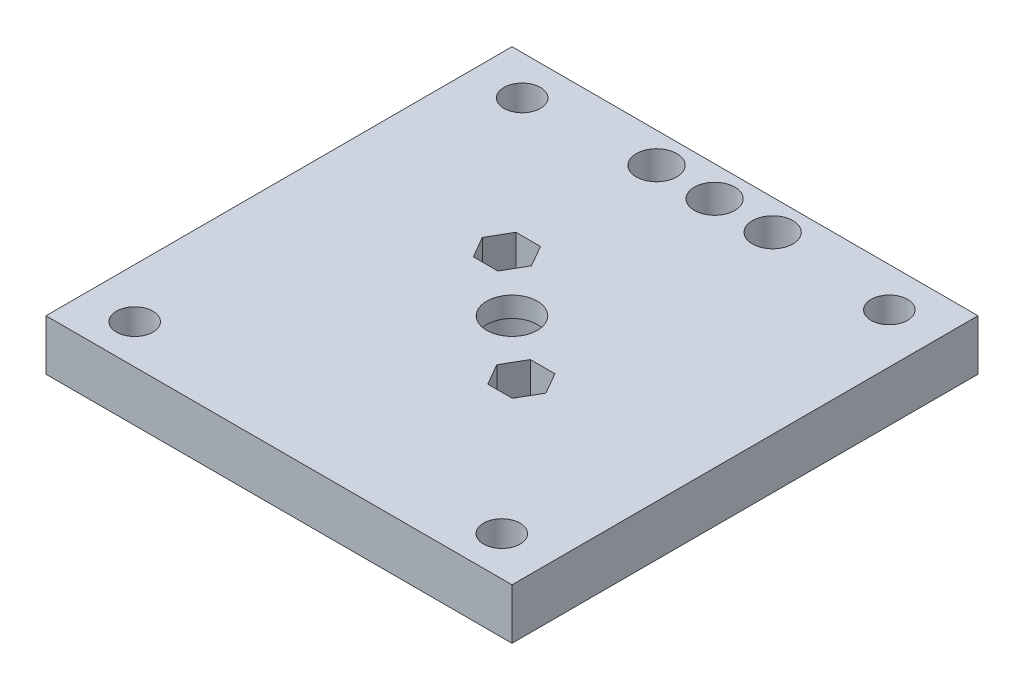
SolidWorks part; units mm, degrees
ref_plane "Front Plane" through (0, 0, 0) normal (0, 0, 1) x (1, 0, 0)
ref_plane "Top Plane" through (0, 0, 0) normal (0, 1, 0) x (1, 0, 0)
ref_plane "Right Plane" through (0, 0, 0) normal (1, 0, 0) x (0, 0, -1)
sketch "Sketch2" plane through (0, 0, 0) normal (0, 1, 0) x (1, 0, 0)
  line L1 (-23, 23) -> (23, 23)
  line L2 (-23, 23) -> (-23, -23)
  line L3 (-23, -23) -> (23, -23)
  line L4 (23, 23) -> (23, -23)
  line L5 (-23, 23) -> (23, -23) construction
  line L6 (-23, -23) -> (23, 23) construction
  point P0 (0, 0)
extrude "Boss-Extrude1" add sketch "Sketch2" along normal blind 5
sketch "Sketch3" plane through (0, 0, 0) normal (0, 1, 0) x (1, 0, 0)
  line L0 (0, 0) -> (-18.12, 0) construction
  line L1 (-18.12, 0) -> (-18.12, 19.125) construction
  line L2 (-18.12, 19.125) -> (18.12, 19.125) construction
  line L3 (18.12, 19.125) -> (18.12, -19.125) construction
  line L4 (18.12, -19.125) -> (-18.12, -19.125) construction
  circle A0 centre (-18.12, 19.125) radius 1.8
  circle A1 centre (18.12, 19.125) radius 1.8
  circle A2 centre (18.12, -19.125) radius 1.8
  circle A3 centre (-18.12, -19.125) radius 1.8
  circle A4 centre (0, 0) radius 2.5
extrude "Cut-Extrude1" cut sketch "Sketch3" along normal blind 5
sketch "Sketch4" plane through (0, 0, 0) normal (0, 1, 0) x (1, 0, 0)
  circle A0 centre (0, 0) radius 4.1
extrude "Cut-Extrude2" cut sketch "Sketch4" along normal blind 3
sketch "Sketch5" plane through (0, 0, 0) normal (0, 1, 0) x (1, 0, 0)
  line L0 (0, 0) -> (0, -4.9397) construction
  line L1 (0, -4.9397) -> (5.8624, -4.9397) construction
  line L2 (0, 0) -> (0, 5.0695) construction
  line L3 (0, 5.0695) -> (-5.733, 5.0695) construction
  line L5 (-3.733, 7.0695) -> (-7.733, 7.0695)
  line L6 (-3.733, 7.0695) -> (-3.733, 3.0695)
  line L7 (-3.733, 3.0695) -> (-7.733, 3.0695)
  line L8 (-7.733, 7.0695) -> (-7.733, 3.0695)
  line L9 (-3.733, 7.0695) -> (-7.733, 3.0695) construction
  line L10 (-3.733, 3.0695) -> (-7.733, 7.0695) construction
  line L11 (3.8624, -2.9397) -> (7.8624, -2.9397)
  line L12 (3.8624, -2.9397) -> (3.8624, -6.9397)
  line L13 (3.8624, -6.9397) -> (7.8624, -6.9397)
  line L14 (7.8624, -2.9397) -> (7.8624, -6.9397)
  line L15 (3.8624, -2.9397) -> (7.8624, -6.9397) construction
  line L16 (3.8624, -6.9397) -> (7.8624, -2.9397) construction
extrude "Boss-Extrude2" add sketch "Sketch5" against normal blind 3
ref_plane "Plane1" through (0, -3, 0) normal (0, -1, 0) x (-1, 0, 0)
sketch "Sketch6" plane through (0, -3, 0) normal (0, -1, 0) x (-1, 0, 0)
  line L0 (5.733, 7.0695) -> (5.733, 5.2308) construction
  line L1 (3.733, 7.0695) -> (7.733, 7.0695) construction
  line L2 (-5.8624, -2.9397) -> (-5.8624, -4.9397) construction
  line L3 (-7.8624, -2.9397) -> (-3.8624, -2.9397) construction
  circle A0 centre (5.733, 5.2308) radius 1
  circle A1 centre (-5.8624, -4.9397) radius 1
extrude "Cut-Extrude3" cut sketch "Sketch6" against normal through all
ref_plane "Plane2" through (0, 5, 0) normal (0, 1, 0) x (1, 0, 0)
sketch "Sketch8" plane through (0, 5, 0) normal (0, 1, 0) x (1, 0, 0)
  line L1 (8.2872, -4.9397) -> (7.0748, -2.8397)
  line L2 (7.0748, -2.8397) -> (4.6499, -2.8397)
  line L3 (4.6499, -2.8397) -> (3.4375, -4.9397)
  line L4 (3.4375, -4.9397) -> (4.6499, -7.0397)
  line L5 (4.6499, -7.0397) -> (7.0748, -7.0397)
  line L6 (7.0748, -7.0397) -> (8.2872, -4.9397)
  line L7 (-3.3081, 5.2308) -> (-4.5206, 7.3308)
  line L8 (-4.5206, 7.3308) -> (-6.9454, 7.3308)
  line L9 (-6.9454, 7.3308) -> (-8.1579, 5.2308)
  line L10 (-8.1579, 5.2308) -> (-6.9454, 3.1308)
  line L11 (-6.9454, 3.1308) -> (-4.5206, 3.1308)
  line L12 (-4.5206, 3.1308) -> (-3.3081, 5.2308)
  circle A0 centre (5.8624, -4.9397) radius 2.1 construction
  circle A1 centre (-5.733, 5.2308) radius 2.1 construction
extrude "Cut-Extrude5" cut sketch "Sketch8" against normal blind 4
sketch "Sketch9" plane through (0, 0, 0) normal (0, 1, 0) x (1, 0, 0)
  line L0 (-5.733, 23) -> (-5.733, 20) construction
  line L1 (23, 23) -> (-23, 23) construction
  line L2 (5.73, 23) -> (5.73, 20) construction
  line L3 (-5.733, 23) -> (0, 23) construction
  line L4 (0, 23) -> (5.73, 23) construction
  circle A0 centre (-5.733, 20) radius 2
  circle A1 centre (5.73, 20) radius 2
  circle A2 centre (0, 20) radius 2
extrude "Cut-Extrude6" cut sketch "Sketch9" along normal through all
